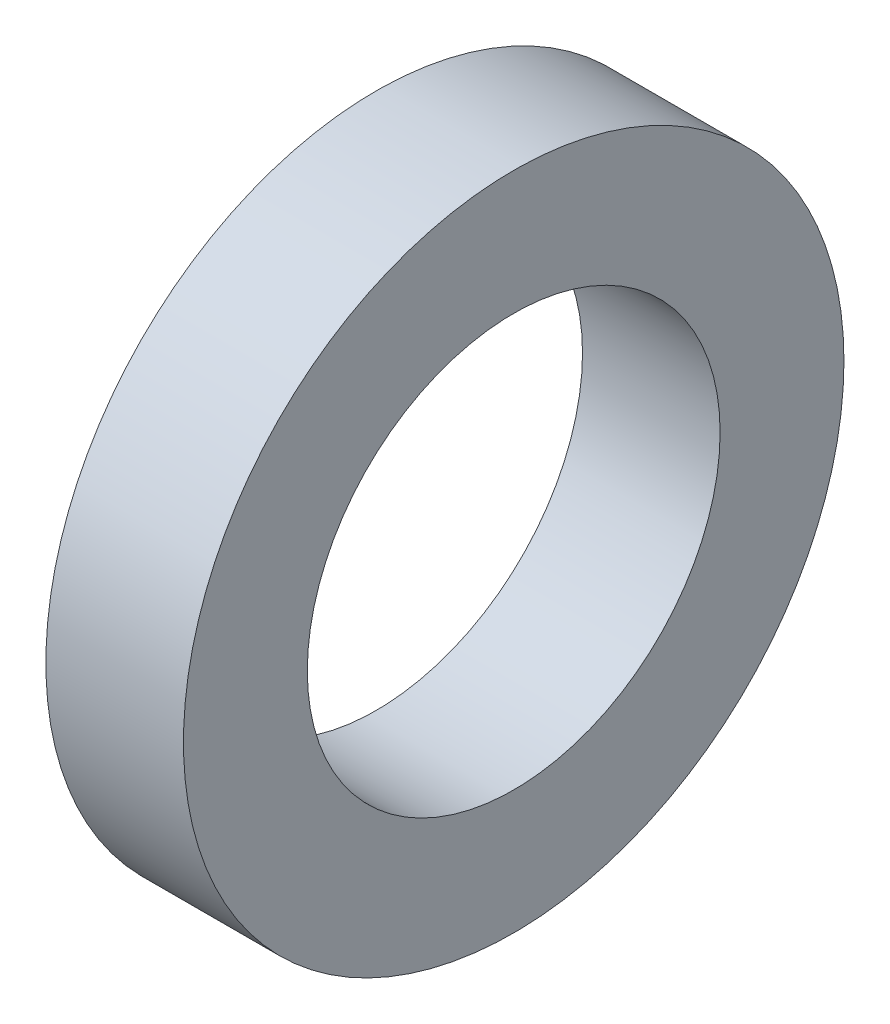
SolidWorks part; units mm, degrees
ref_plane "Front" through (0, 0, 0) normal (0, 0, 1) x (1, 0, 0)
ref_plane "Top" through (0, 0, 0) normal (0, 1, 0) x (1, 0, 0)
ref_plane "Right" through (0, 0, 0) normal (1, 0, 0) x (0, 0, -1)
sketch "Эскиз1" plane through (0, 0, 0) normal (1, 0, 0) x (0, 0, -1)
  circle A0 centre (0, 0) radius 7.5
  circle A1 centre (0, 0) radius 12
  dimension "D1" = 24
  dimension "D2" = 15
extrude "Бобышка-Вытянуть1" add sketch "Эскиз1" along normal blind 5
